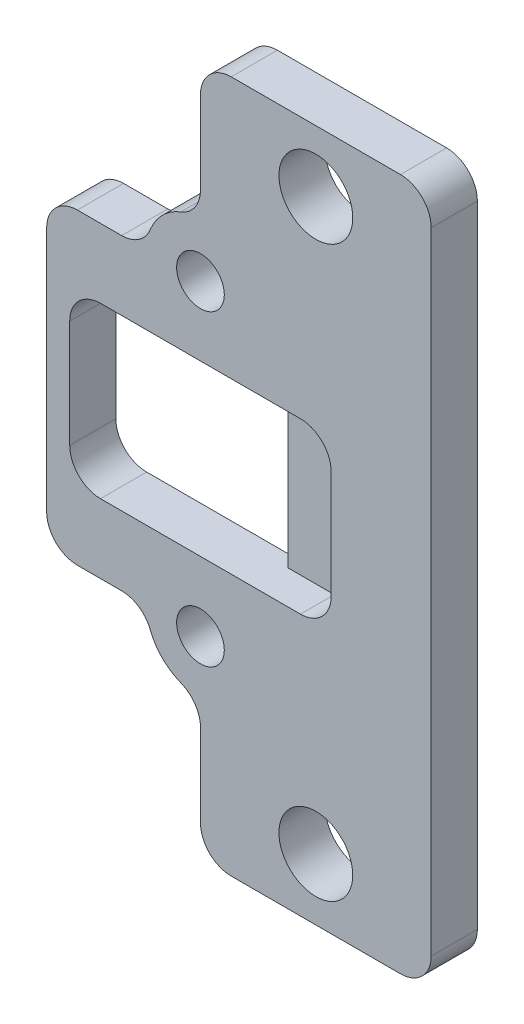
SolidWorks part; units mm, degrees
material "ABS"
ref_plane "正面" through (0, 0, 0) normal (1, 0, 0) x (0, 1, 0)
ref_plane "平面" through (0, 0, 0) normal (0, 0, 1) x (0, 1, 0)
ref_plane "右側面" through (0, 0, 0) normal (0, 1, 0) x (-1, 0, 0)
sketch "ｽｹｯﾁ1" plane through (0, 0, 0) normal (0, 0, 1) x (0, 1, 0)
  line L1 (-22.5, -7.5) -> (22.5, -7.5)
  line L2 (-22.5, -7.5) -> (-22.5, 7.5)
  line L3 (-22.5, 7.5) -> (22.5, 7.5)
  line L4 (22.5, -7.5) -> (22.5, 7.5)
  line L5 (-22.5, -7.5) -> (22.5, 7.5) construction
  line L6 (-22.5, 7.5) -> (22.5, -7.5) construction
  line L7 (-10, 17.5) -> (10, 17.5)
  line L8 (-10, 17.5) -> (-10, 7.5)
  line L9 (-10, 7.5) -> (10, 7.5)
  line L10 (10, 17.5) -> (10, 7.5)
  line L11 (-10, 17.5) -> (10, 7.5) construction
  line L12 (-10, 7.5) -> (10, 17.5) construction
  line L13 (-5.5, -1) -> (5.5, -1)
  line L14 (-5.5, -1) -> (-5.5, 16)
  line L15 (-5.5, 16) -> (5.5, 16)
  line L16 (5.5, -1) -> (5.5, 16)
  line L17 (-5.5, -1) -> (5.5, 16) construction
  line L18 (-5.5, 16) -> (5.5, -1) construction
  circle A0 centre (-10, 7.5) radius 3.5
  circle A1 centre (10, 7.5) radius 3.5
  circle A2 centre (-10, 7.5) radius 1.55
  circle A3 centre (10, 7.5) radius 1.55
  point P0 (0, 0)
  point P6 (0, 12.5)
  point P17 (0, 7.5)
  point P22 (0, 0)
  point P23 (0, 17.5)
  point P24 (0, 0)
  point P25 (0, 17.5)
  point P26 (0, 0)
  point P27 (0, 0)
  point P28 (0, 0)
  point P29 (0, 0)
  point P30 (0, 0)
  point P31 (0, 0)
  point P32 (0, 0)
  point P33 (0, 0)
  point P34 (0, 0)
  point P35 (0, 0)
  dimension "D5" = 7
  dimension "D6" = 3.1
  dimension "D1" = 45
  dimension "D2" = 15
  dimension "D3" = 10
  dimension "D4" = 20
  dimension "D7" = 11
  dimension "D8" = 17
  dimension "D9" = 1.5
extrude "ﾎﾞｽ - 押し出し1" add sketch "ｽｹｯﾁ1" along normal blind 3 contours A1 L3 L16 L13 L14 L9 A0 L2 L1 L4 | A1 L10 L7 L8 A0 L9 L14 L15 L16 L3 | A2 L9 A0 L8 | A2 L8 A0 L3 | A2 L3 A0 L9 | A3 L10 A1 L9 | A3 L3 A1 L10 | A3 L9 A1 L3
sketch "ｽｹｯﾁ2" plane through (0, 0, 3) normal (0, 0, 1) x (1, 0, 0)
  line L0 (7.5, -22.5) -> (7.5, 22.5) construction
  line L1 (7.5, 22.5) -> (-7.5, 22.5) construction
  point P0 (0, -18.5)
  point P1 (0, 18.5)
  point P4 (7.5, 0)
  point P5 (0, 0)
  point P8 (0, 22.5)
  dimension "D1" = 37
  dimension "D2" = 18.5
hole_wizard "M4 すきま穴1" positions "ｽｹｯﾁ2" profile "ｽｹｯﾁ3" hole size "M4" standard "JIS" end condition through all
sketch "ｽｹｯﾁ3" plane through (0, -18.5, 3) normal (1, 0, 0) x (0, -1, 0)
  line L0 (0, 0) -> (0, 3)
  line L1 (0, 3) -> (2.4, 3)
  line L2 (2.4, 3) -> (2.4, 0)
  line L5 (2.4, 0) -> (0, 0)
  line L11 (0, -6.35) -> (0, 107.95) construction
  dimension "通し穴の直径" = 4.8
  dimension "通し穴の深さ" = 3
sketch "ｽｹｯﾁ5" plane through (0, 0, 0) normal (0, 0, -1) x (1, 0, 0)
  line L0 (1, -5.5) -> (-16, -5.5) construction
  line L1 (1, 5.5) -> (-4, 5.5)
  line L2 (1, 5.5) -> (1, -5.5)
  line L3 (1, -5.5) -> (-4, -5.5)
  line L4 (-4, 5.5) -> (-4, -5.5)
  line L5 (1, 5.5) -> (-4, -5.5) construction
  line L6 (1, -5.5) -> (-4, 5.5) construction
  point P4 (-1.5, 0)
  dimension "D1" = 5
extrude "ﾎﾞｽ - 押し出し2" add sketch "ｽｹｯﾁ5" against normal blind 0.8
fillet "ﾌｨﾚｯﾄ6" radius 2 14 edges at (-16, -5.5, 1.5) (-16, 5.5, 1.5) (1, 5.5, 1.9) (1, -5.5, 1.9) (-11, -10, 1.5) (-17.5, -10, 1.5) (-17.5, 10, 1.5) (-11, 10, 1.5) (-7.5, 22.5, 1.5) (7.5, 22.5, 1.5) (7.5, -22.5, 1.5) (-7.5, -22.5, 1.5) (-7.5, 13.5, 1.5) (-7.5, -13.5, 1.5)
